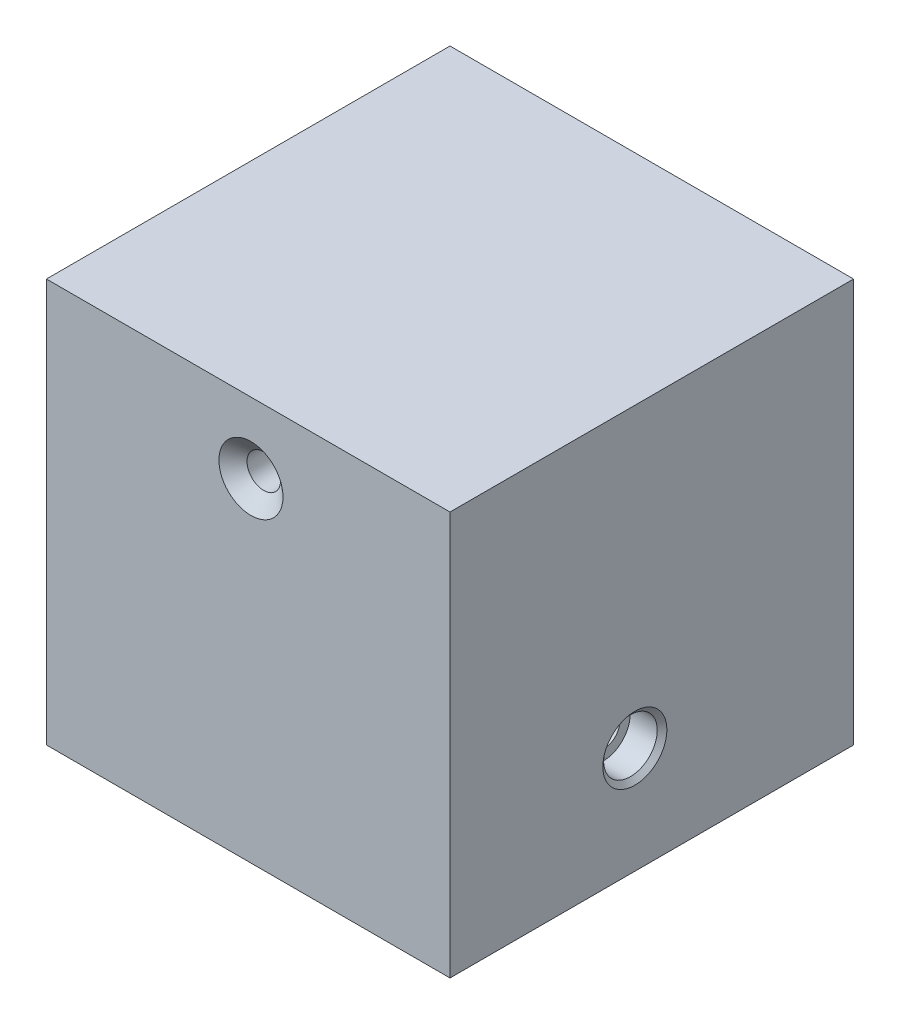
SolidWorks part; units mm, degrees
ref_plane "Front" through (0, 0, 0) normal (0, 0, 1) x (1, 0, 0)
ref_plane "Top" through (0, 0, 0) normal (0, 1, 0) x (1, 0, 0)
ref_plane "Right" through (0, 0, 0) normal (1, 0, 0) x (0, 0, -1)
sketch "Sketch1" plane through (0, 0, 0) normal (0, 0, 1) x (1, 0, 0)
  line L1 (0, 0) -> (101.6, 0)
  line L2 (0, 0) -> (0, 101.6)
  line L3 (0, 101.6) -> (101.6, 101.6)
  line L4 (101.6, 0) -> (101.6, 101.6)
  dimension "D1" = 101.6
  dimension "D2" = 101.6
extrude "Boss-Extrude1" add sketch "Sketch1" along normal blind 101.6
hole_wizard "CSK for 5/16 Flat Head Machine Screw (100)1" positions "Sketch2" profile "Sketch3" countersink size "5/16" standard "ANSI Inch" end condition through all
sketch "Sketch2" plane through (0, 0, 101.6) normal (0, 0, 1) x (1, 0, 0)
  point P0 (51.4901, 83.8415)
sketch "Sketch3" plane through (51.4901, 83.8415, 101.6) normal (1, 0, 0) x (0, -1, 0)
  line L0 (0, 0) -> (0, 101.6)
  line L1 (0, 101.6) -> (8.0645, 101.6)
  line L2 (4.2164, 98.3711) -> (4.2164, 3.2289)
  line L3 (4.2164, 3.2289) -> (8.0645, 0)
  line L5 (8.0645, 0) -> (0, 0)
  line L6 (-4.2164, 3.2289) -> (-8.0645, 0) construction
  line L7 (8.0645, 101.6) -> (4.2164, 98.3711)
  line L8 (-8.0645, 101.6) -> (-4.2164, 98.3711) construction
  line L11 (0, -6.35) -> (0, 107.95) construction
  dimension "Thru Hole Dia." = 8.4328
  dimension "Thru Hole Depth" = 101.6
  dimension "Near C'Sink Dia." = 16.129
  dimension "Near C'Sink Angle" = 100
  dimension "Far C'Sink Dia." = 16.129
  dimension "Far C'Sink Angle" = 100
hole_wizard "CBORE for 5/16 Socket Head Cap Screw1" positions "Sketch4" profile "Sketch5" counterbore size "5/16" standard "ANSI Inch" end condition through all
sketch "Sketch4" plane through (101.6, 0, 0) normal (1, 0, 0) x (0, 0, -1)
  point P0 (-55.0625, 26.8232)
sketch "Sketch5" plane through (101.6, 26.8232, 55.0625) normal (0, 1, 0) x (0, 0, -1)
  line L0 (0, 0) -> (0, 101.6)
  line L1 (0, 101.6) -> (4.2164, 101.6)
  line L3 (4.2164, 101.6) -> (4.2164, 7.9375)
  line L4 (6.7475, 7.9375) -> (4.2164, 7.9375)
  line L5 (6.7475, 7.9375) -> (6.7475, 1.1051)
  line L6 (6.7475, 1.1051) -> (8.0645, 0)
  line L7 (8.0645, 0) -> (0, 0)
  line L8 (-6.7475, 1.1051) -> (-8.0645, 0) construction
  line L11 (0, -6.35) -> (0, 107.95) construction
  dimension "Thru Hole Dia." = 8.4328
  dimension "Thru Hole Depth" = 101.6
  dimension "C'Bore Dia." = 13.495
  dimension "C'Bore Depth" = 7.9375
  dimension "Near C'Sink Dia." = 16.129
  dimension "Near C'Sink Angle" = 100
sketch "Sketch6" plane through (0, 0, 0) normal (-1, 0, 0) x (0, 0, 1)
  circle A0 centre (55.0625, 26.8232) radius 6.9228
extrude "Cut-Extrude1" cut sketch "Sketch6" against normal blind 12.7
chamfer "Chamfer2" distance 2.54 angle 45 1 edges at (0, 26.8232, 61.9853)
